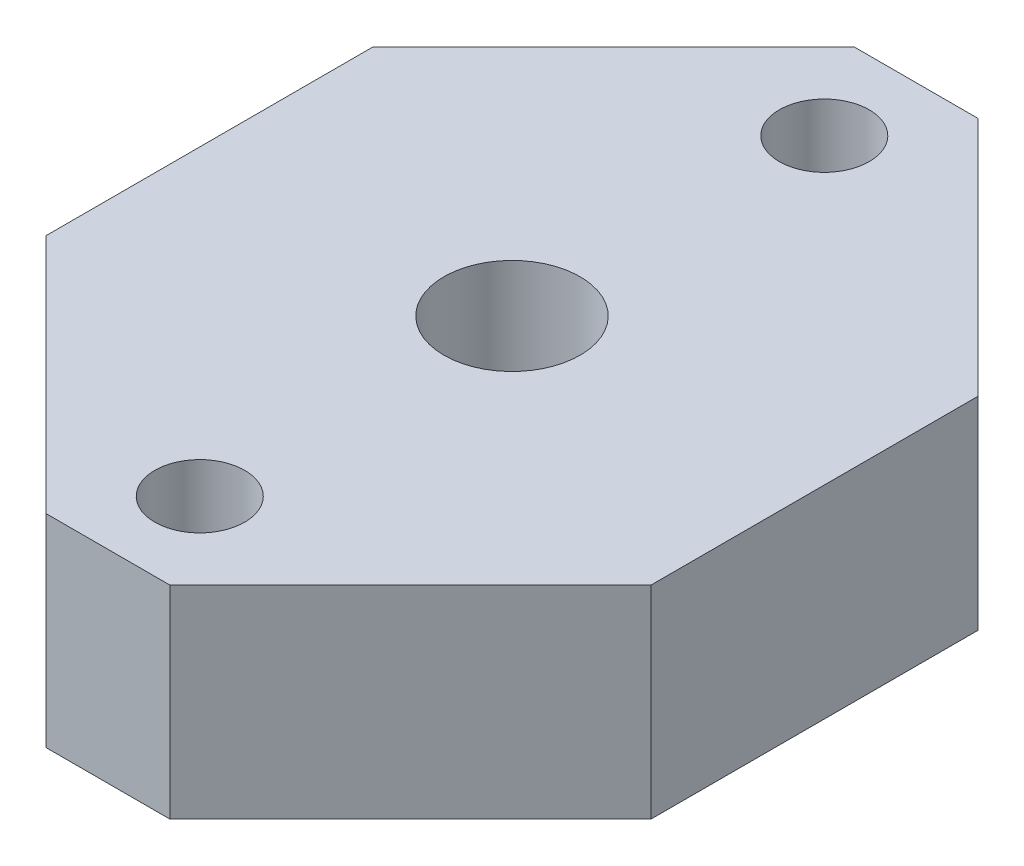
SolidWorks part; units mm, degrees
ref_plane "Front Plane" through (0, 0, 0) normal (0, 0, 1) x (1, 0, 0)
ref_plane "Top Plane" through (0, 0, 0) normal (0, 1, 0) x (1, 0, 0)
ref_plane "Right Plane" through (0, 0, 0) normal (1, 0, 0) x (0, 0, -1)
sketch "Sketch1" plane through (0, 0, 0) normal (0, 1, 0) x (1, 0, 0)
  line L0 (17.78, 47.498) -> (17.78, 42.1005) construction
  line L1 (0, 47.498) -> (35.56, 47.498)
  line L2 (0, 47.498) -> (0, 0)
  line L3 (0, 0) -> (35.56, 0)
  line L4 (35.56, 47.498) -> (35.56, 0)
  line L5 (17.78, 23.749) -> (35.56, 23.749) construction
  line L6 (17.78, 0) -> (17.78, 5.3975) construction
  line L7 (17.78, 5.3975) -> (17.78, 42.1005) construction
  circle A0 centre (17.78, 42.1005) radius 2.6416
  circle A1 centre (17.78, 5.3975) radius 2.6416
  circle A2 centre (17.78, 23.749) radius 4
  dimension "D4" = 5.2832
  dimension "D5" = 8
  dimension "D1" = 47.498
  dimension "D2" = 35.56
  dimension "D3" = 36.703
extrude "Boss-Extrude1" add sketch "Sketch1" along normal blind 11.9126
sketch "Sketch2" plane through (0, 11.9126, 0) normal (0, 1, 0) x (1, 0, 0)
  line L0 (14.1421, 0) -> (0, 14.1421)
  line L1 (0, 0) -> (35.56, 0) construction
  line L2 (0, 47.498) -> (0, 0) construction
  line L3 (0, 14.1421) -> (0, 0)
  line L4 (0, 0) -> (14.1421, 0)
  line L5 (0, 23.749) -> (35.56, 23.749) construction
  line L6 (35.56, 0) -> (35.56, 47.498) construction
  line L7 (21.4179, 0) -> (35.56, 14.1421)
  line L8 (35.56, 14.1421) -> (35.56, 0)
  line L9 (35.56, 0) -> (21.4179, 0)
  line L10 (21.4179, 47.498) -> (35.56, 47.498)
  line L11 (35.56, 47.498) -> (0, 47.498) construction
  line L12 (35.56, 47.498) -> (35.56, 33.3559)
  line L13 (35.56, 33.3559) -> (21.4179, 47.498)
  line L14 (14.1421, 47.498) -> (0, 33.3559)
  line L15 (0, 33.3559) -> (0, 47.498)
  line L16 (0, 47.498) -> (14.1421, 47.498)
  point P23 (7.2234, 47.498)
  point P26 (0, 0)
  point P27 (8.2267, 47.498)
  point P28 (12.1816, 0)
  dimension "D1" = 20
extrude "Cut-Extrude1" cut sketch "Sketch2" against normal through all
